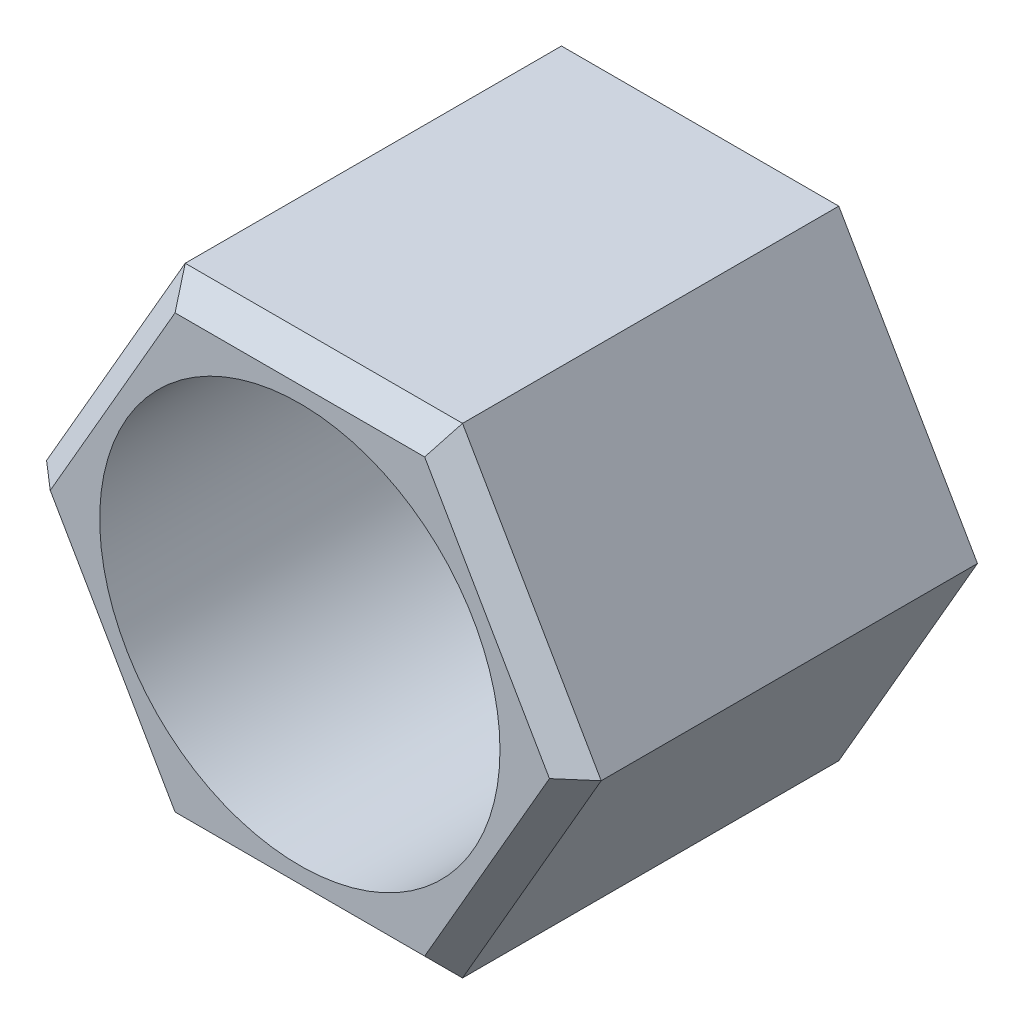
SolidWorks part; units mm, degrees
ref_plane "Front Plane" through (0, 0, 0) normal (0, 0, 1) x (1, 0, 0)
ref_plane "Top Plane" through (0, 0, 0) normal (0, 1, 0) x (1, 0, 0)
ref_plane "Right Plane" through (0, 0, 0) normal (1, 0, 0) x (0, 0, -1)
sketch "Sketch2" plane through (0, 0, 0) normal (0, 0, 1) x (1, 0, 0)
  line L1 (8.7988, 0) -> (4.3994, 7.62)
  line L2 (4.3994, 7.62) -> (-4.3994, 7.62)
  line L3 (-4.3994, 7.62) -> (-8.7988, 0)
  line L4 (-8.7988, 0) -> (-4.3994, -7.62)
  line L5 (-4.3994, -7.62) -> (4.3994, -7.62)
  line L6 (4.3994, -7.62) -> (8.7988, 0)
  circle A0 centre (0, 0) radius 7.62 construction
  dimension "D1" = 15.24
extrude "Extrude1" add sketch "Sketch2" along normal blind 12.7
sketch "Sketch4" plane through (0, 0, 12.7) normal (0, 0, 1) x (1, 0, 0)
  circle A0 centre (0, 0) radius 6.35
  dimension "D1" = 12.7
extrude "Cut-Extrude1" cut sketch "Sketch4" against normal through all
chamfer "Chamfer2" distance 0.762 angle 45 6 edges at (0, 7.62, 12.7) (-6.5991, 3.81, 12.7) (-6.5991, -3.81, 12.7) (0, -7.62, 12.7) (6.5991, -3.81, 12.7) (6.5991, 3.81, 12.7)
